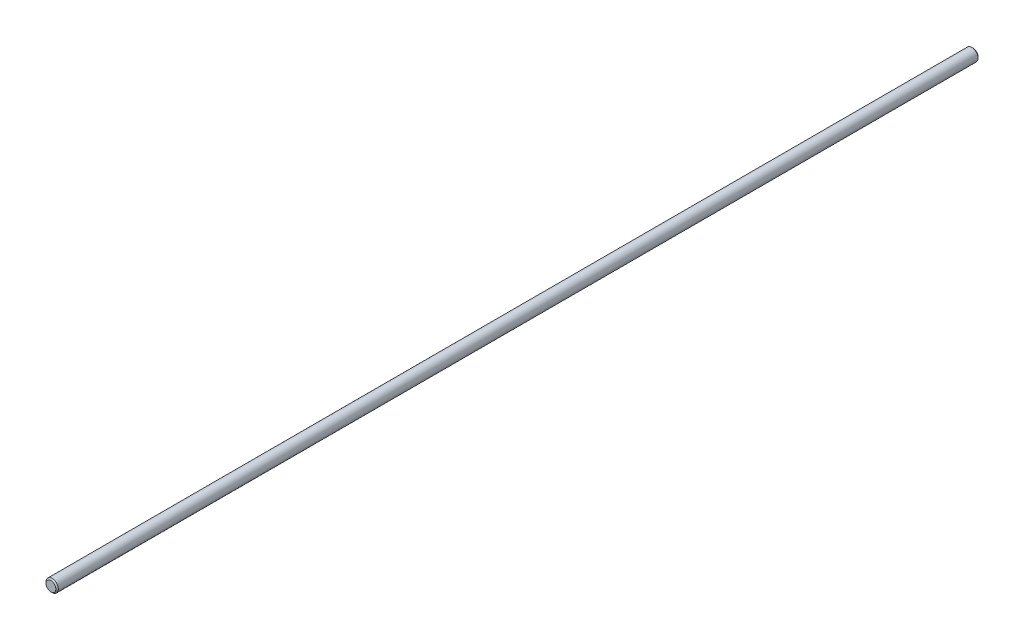
SolidWorks part; units mm, degrees
ref_plane "Front" through (0, 0, 0) normal (0, 0, 1) x (1, 0, 0)
ref_plane "Top" through (0, 0, 0) normal (0, 1, 0) x (1, 0, 0)
ref_plane "Right" through (0, 0, 0) normal (1, 0, 0) x (0, 0, -1)
sketch "Sketch1" plane through (0, 0, 0) normal (0, 0, 1) x (1, 0, 0)
  circle A0 centre (0, 0) radius 8
  dimension "D1" = 16
extrude "Extrude1" add sketch "Sketch1" along normal mid plane 1200
chamfer "Chamfer1" distance 1.6 angle 45 2 edges at (8, 0, -600) (8, 0, 600)
equation "\"D1@Chamfer1\" = \"D1@Sketch1\" * .1"
